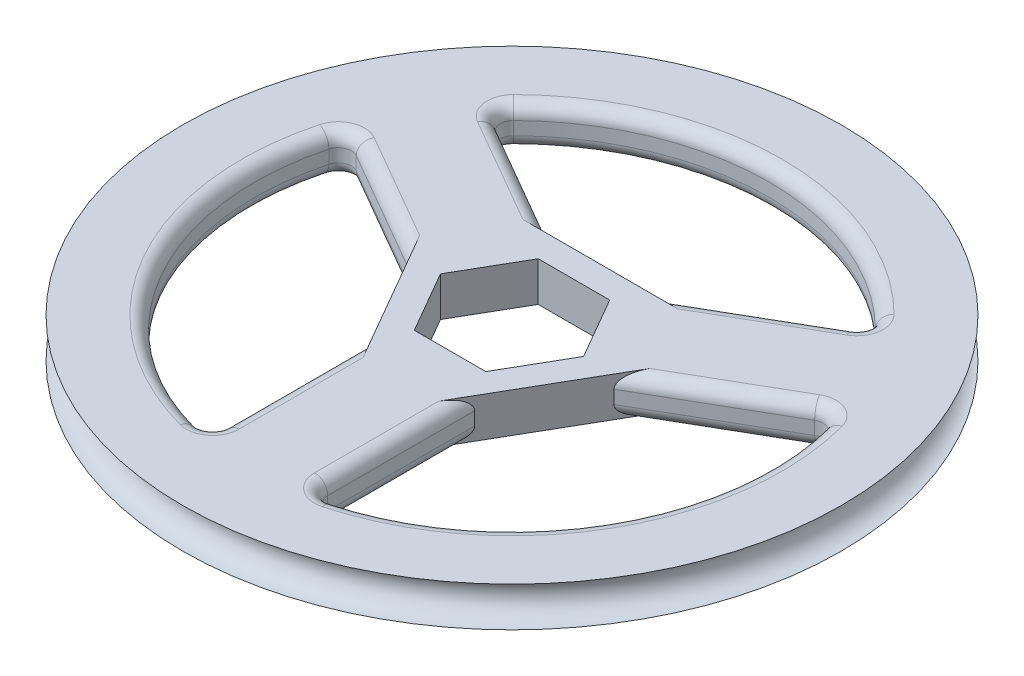
SolidWorks part; units mm, degrees
ref_plane "Front Plane" through (0, 0, 0) normal (0, 0, 1) x (1, 0, 0)
ref_plane "Top Plane" through (0, 0, 0) normal (0, 1, 0) x (1, 0, 0)
ref_plane "Right Plane" through (0, 0, 0) normal (1, 0, 0) x (0, 0, -1)
sketch "Sketch1" plane through (0, 0, 0) normal (0, 1, 0) x (1, 0, 0)
  line L0 (-6.8924, 0) -> (6.8924, 0) construction
  line L1 (3.4462, 5.969) -> (-3.4462, 5.969)
  line L2 (-3.4462, 5.969) -> (-6.8924, 0)
  line L3 (-6.8924, 0) -> (-3.4462, -5.969)
  line L4 (-3.4462, -5.969) -> (3.4462, -5.969)
  line L5 (3.4462, -5.969) -> (6.8924, 0)
  line L6 (6.8924, 0) -> (3.4462, 5.969)
  line L7 (-4.9127, -8.509) -> (4.9127, -8.509)
  line L8 (4.9127, -8.509) -> (9.8253, 0)
  line L9 (9.8253, 0) -> (4.9127, 8.509)
  line L10 (4.9127, 8.509) -> (-4.9127, 8.509)
  line L11 (-4.9127, 8.509) -> (-9.8253, 0)
  line L12 (-9.8253, 0) -> (-4.9127, -8.509)
  line L13 (-4.9127, -8.509) -> (-4.9127, -24.2728)
  line L14 (4.9127, -8.509) -> (4.9127, -24.2728)
  line L15 (-4.9127, 8.509) -> (-18.5646, 16.3909)
  line L16 (-9.8253, 0) -> (-23.4772, 7.8819)
  line L17 (9.8253, 0) -> (23.4772, 7.8819)
  line L18 (4.9127, 8.509) -> (18.5646, 16.3909)
  circle A0 centre (0, 0) radius 31.75
  circle A1 centre (0, 0) radius 5.969 construction
  circle A2 centre (0, 0) radius 24.765
  circle A3 centre (0, 0) radius 2.2225
  point P22 (0, 0)
  point P30 (0, 0)
  dimension "D1" = 11.938
  dimension "D2" = 63.5
  dimension "D4" = 49.53
  dimension "D5" = 3
  dimension "D6" = 4.445
  dimension "D3" = 2.54
extrude "Boss-Extrude1" add sketch "Sketch1" along normal blind 3.81 contours A0 A2 | L13 A2 L14 L7 | L15 A2 L16 L11 | L17 A2 L18 L9 | L11 L12 L7 L8 L9 L10 L6 L5 L4 L3 L2 L1
sketch "Sketch5" plane through (0, 0, 0) normal (1, 0, 0) x (0, 0, -1)
  line L0 (-31.75, 3.81) -> (0, 3.81) construction
  line L1 (-31.75, 0) -> (0, 0) construction
  line L2 (-31.75, 3.81) -> (-31.75, 0)
  line L3 (0, 3.81) -> (0, 0)
  arc A0 (-31.75, 3.81) -> (-31.75, 0) centre (-31.75, 1.905) cw
revolve "Cut-Revolve4" cut sketch "Sketch5" angle 360 about L3
fillet "Fillet2" radius 1.27 24 edges at (-11.7386, 0, -12.45) (-11.7386, 3.81, -12.45) (11.7386, 0, -12.45) (11.7386, 3.81, -12.45) (16.6513, 0, -3.941) (16.6513, 3.81, -3.941) (4.9127, 0, 16.3909) (4.9127, 3.81, 16.3909) (-4.9127, 0, 16.3909) (-4.9127, 3.81, 16.3909) (-16.6513, 0, -3.941) (-16.6513, 3.81, -3.941) (-18.5646, 1.905, -16.3909) (0, 3.81, -24.765) (0, 0, -24.765) (18.5646, 1.905, -16.3909) (23.4772, 1.905, -7.8819) (21.4471, 3.81, 12.3825) (21.4471, 0, 12.3825) (4.9127, 1.905, 24.2728) (-4.9127, 1.905, 24.2728) (-21.4471, 3.81, 12.3825) (-21.4471, 0, 12.3825) (-23.4772, 1.905, -7.8819)
